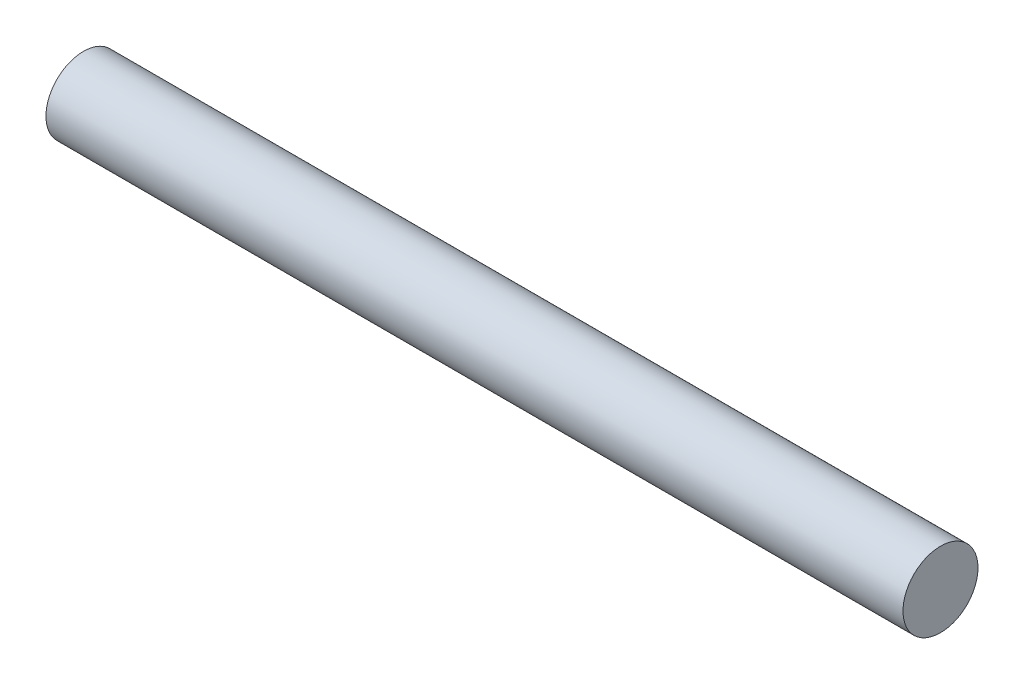
SolidWorks part; units mm, degrees
ref_plane "Front Plane" through (0, 0, 0) normal (0, 0, 1) x (1, 0, 0)
ref_plane "Top Plane" through (0, 0, 0) normal (0, 1, 0) x (1, 0, 0)
ref_plane "Right Plane" through (0, 0, 0) normal (1, 0, 0) x (0, 0, -1)
sketch "Sketch1" plane through (0, 0, 0) normal (1, 0, 0) x (0, 0, -1)
  circle A0 centre (0, 0) radius 3
extrude "Boss-Extrude1" add sketch "Sketch1" along normal blind 68.55
